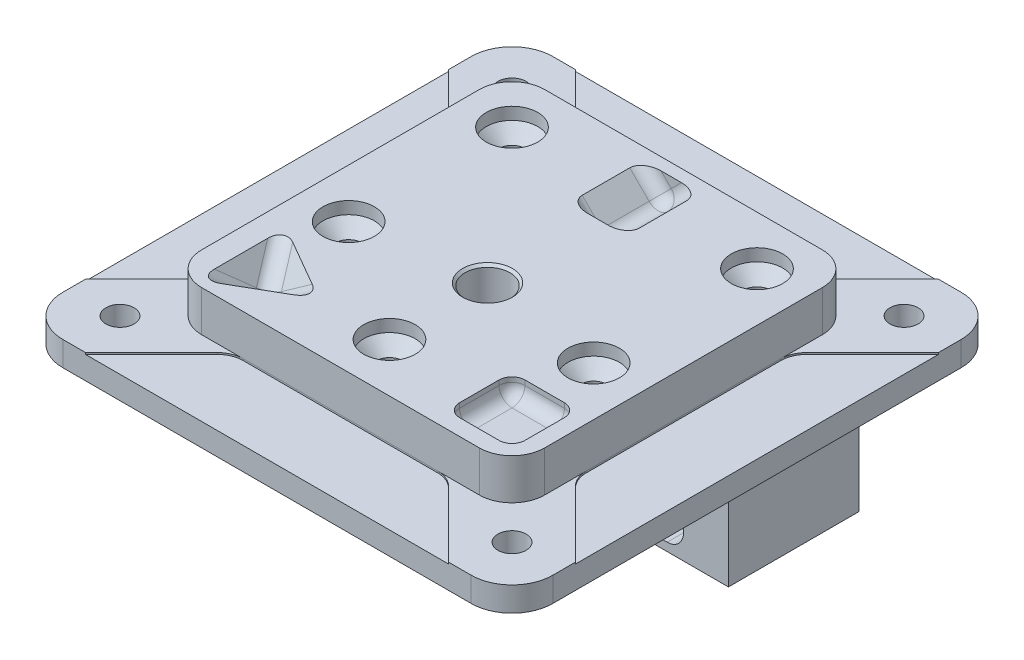
SolidWorks part; units mm, degrees
material "Ti-6Al-4VSolution treated and aged (SS)"
ref_plane "Front" through (0, 0, 0) normal (0, 0, 1) x (1, 0, 0)
ref_plane "Top" through (0, 0, 0) normal (0, 1, 0) x (1, 0, 0)
ref_plane "Right" through (0, 0, 0) normal (1, 0, 0) x (0, 0, -1)
sketch "Sketch6" plane through (0, 0, 0) normal (0, 1, 0) x (1, 0, 0)
  line L0 (8, 0) -> (-8, 0) construction
  line L1 (30, -30) -> (-30, -30)
  line L2 (30, -30) -> (30, 30)
  line L3 (30, 30) -> (-30, 30)
  line L4 (-30, -30) -> (-30, 30)
  line L6 (30, 30) -> (-30, -30) construction
  point P6 (0, 0)
  point P10 (0, 0)
  dimension "D1" = 60
extrude "plate" add sketch "Sketch6" along normal blind 8
sketch "Sketch7" plane through (0, 8, 0) normal (0, 1, 0) x (1, 0, 0)
  line L12 (21, -21) -> (21, 21)
  line L13 (21, 21) -> (-21, 21)
  line L14 (-21, 21) -> (-21, -21)
  line L15 (-21, -21) -> (21, -21)
  line L16 (21, -21) -> (21, 21)
  line L17 (21, 21) -> (-21, 21)
  line L18 (-21, 21) -> (-21, -21)
  line L19 (-21, -21) -> (21, -21)
  line L20 (30, -30) -> (30, 30)
  line L21 (30, 30) -> (-30, 30)
  line L22 (-30, 30) -> (-30, -30)
  line L23 (-30, -30) -> (30, -30)
  line L24 (30, -30) -> (30, 30)
  line L25 (30, 30) -> (-30, 30)
  line L26 (-30, 30) -> (-30, -30)
  line L27 (-30, -30) -> (30, -30)
  dimension "D1" = 9
  dimension "D2" = 0
extrude "top hat" cut sketch "Sketch7" against normal blind 5
sketch "Sketch8" plane through (0, 8, 0) normal (0, 1, 0) x (1, 0, 0)
  line L0 (15, -15) -> (-15, -15) construction
  line L1 (0, -15) -> (0, 15) construction
  line L2 (21, 0) -> (18.1749, 0) construction
  line L3 (21, -21) -> (21, 21) construction
  point P9 (0, 0)
  point P10 (0, -3)
  dimension "D1" = 30
  dimension "D2" = 12
sketch3d "3DSketch1"
  line L0 (-18.1815, 8, 20.5104) -> (-18.1815, 8, 9.4896)
  line L1 (-18.1815, 8, 9.4896) -> (-8.6371, 8, 15)
  line L2 (-8.6371, 8, 15) -> (-18.1815, 8, 20.5104)
  line L3 (-18.1815, 8, 20.5104) -> (-15, 3.5007, 15)
  line L4 (-18.1815, 8, 9.4896) -> (-15, 3.5007, 15)
  line L5 (-8.6371, 8, 15) -> (-15, 3.5007, 15)
  line L6 (-15, 3.5007, 15) -> (-15, 8, 15)
  line L7 (-18.1815, 8, 20.5104) -> (-13.4093, 8, 12.2448)
  line L8 (-8.6371, 8, 15) -> (-18.1815, 8, 15)
  point P8 (-18.1815, 8, 15)
  point P9 (-13.4093, 8, 12.2448)
  dimension "D1" = 4.4993
ref_plane "cube" through (-8.3497, -5.9042, 0) normal (0.8165, 0.5774, 0) x (0, 0, -1)
ref_plane "Plane2" through (0, 0, -15) normal (0, 0, 1) x (1, 0, 0)
sketch "Sketch13" plane through (0, 3, 0) normal (0, 1, 0) x (1, 0, 0)
  line L1 (24, -24) -> (-24, -24)
  line L2 (24, -24) -> (24, 24)
  line L3 (24, 24) -> (-24, 24)
  line L4 (-24, -24) -> (-24, 24)
  line L5 (-24, -24) -> (24, 24) construction
  point P4 (0, 0)
  dimension "D1" = 48
hole_wizard "#8-32 Tapped Hole1" positions "3DSketch3" profile "Sketch16" tap size "#8-32" standard "Ansi Inch" end condition through all
sketch3d "3DSketch3"
  point P0 (-24, 3, -24)
  point P3 (24, 3, -24)
  point P6 (24, 3, 24)
  point P9 (-24, 3, 24)
sketch "Sketch16" plane through (-24, 3, -24) normal (1, 0, 0) x (0, 0, 1)
  line L0 (0, 0) -> (0, 3)
  line L1 (0, 3) -> (1.7272, 3)
  line L2 (1.7272, 3) -> (1.7272, 0)
  line L5 (1.7272, 0) -> (0, 0)
  line L11 (0, -6.35) -> (0, 107.95) construction
  dimension "Thru Tap Drill Dia." = 3.4544
  dimension "Thru Tap Drill Depth" = 3
cosmetic thread "Hole Thread17" parameters "D2"=4.1656
cosmetic thread "Hole Thread18" parameters "D2"=4.1656
cosmetic thread "Hole Thread19" parameters "D2"=4.1656
cosmetic thread "Hole Thread20" parameters "D2"=4.1656
fillet "Fillet2" radius 5 4 edges at (-30, 1.5, -30) (-30, 1.5, 30) (30, 1.5, 30) (30, 1.5, -30)
fillet "Fillet3" radius 4 4 edges at (-21, 5.5, -21) (21, 5.5, -21) (21, 5.5, 21) (-21, 5.5, 21)
sketch "Sketch15" plane through (0, 3, 0) normal (0, 1, 0) x (1, 0, 0)
  line L0 (30, 22.2218) -> (30, -22.2218)
  line L1 (30, 22.2218) -> (21.9299, 14.1518)
  line L2 (30, -22.2218) -> (21.9299, -14.1518)
  line L3 (21, -17) -> (21, 17) construction
  line L4 (21, -11.9067) -> (21, 11.9067)
  line L6 (24, -24) -> (27.8891, -20.1109) construction
  line L7 (21, 0) -> (14.7049, 0) construction
  line L8 (24, -24) -> (-24, 24) construction
  line L9 (24, 24) -> (-24, -24) construction
  line L10 (11.9067, -21) -> (-11.9067, -21)
  line L11 (22.2218, -30) -> (14.1518, -21.9299)
  line L12 (-22.2218, -30) -> (-14.1518, -21.9299)
  line L13 (-22.2218, -30) -> (22.2218, -30)
  line L14 (-30, -22.2218) -> (-30, 22.2218)
  line L15 (-30, 22.2218) -> (-21.9299, 14.1518)
  line L16 (-21, 11.9067) -> (-21, -11.9067)
  line L17 (-30, -22.2218) -> (-21.9299, -14.1518)
  line L18 (22.2218, 30) -> (-22.2218, 30)
  line L19 (-22.2218, 30) -> (-14.1518, 21.9299)
  line L20 (-11.9067, 21) -> (11.9067, 21)
  line L21 (22.2218, 30) -> (14.1518, 21.9299)
  line L23 (-30, 25) -> (-30, -25) construction
  arc A0 (21, 11.9067) -> (21.9299, 14.1518) centre (24.175, 11.9067) cw
  arc A1 (21, -11.9067) -> (21.9299, -14.1518) centre (24.175, -11.9067) ccw
  arc A2 (11.9067, -21) -> (14.1518, -21.9299) centre (11.9067, -24.175) cw
  arc A3 (-11.9067, -21) -> (-14.1518, -21.9299) centre (-11.9067, -24.175) ccw
  arc A4 (-21, 11.9067) -> (-21.9299, 14.1518) centre (-24.175, 11.9067) ccw
  arc A5 (-21, -11.9067) -> (-21.9299, -14.1518) centre (-24.175, -11.9067) cw
  arc A6 (-11.9067, 21) -> (-14.1518, 21.9299) centre (-11.9067, 24.175) cw
  arc A7 (11.9067, 21) -> (14.1518, 21.9299) centre (11.9067, 24.175) ccw
  point P15 (21, -13.2218)
  point P20 (30, 0)
  point P32 (0, -30)
  dimension "D3" = 3.175
  dimension "D1" = 45
  dimension "D2" = 5.5
extrude "Extrude8" cut sketch "Sketch15" against normal blind 0.2
ref_plane "post z center" through (0, 0, 0) normal (0, 0, 1) x (1, 0, 0)
ref_plane "Plane5" through (-11, 0, 0) normal (1, 0, 0) x (0, 0, -1)
sketch "Sketch24" plane through (-11, 0, 0) normal (1, 0, 0) x (0, 0, -1)
  line L0 (0.7631, 2.8) -> (23.4869, 2.8)
  line L1 (-8, 2.8) -> (0.7631, 2.8)
  line L2 (30, 2.8) -> (21.9299, 2.8) construction
  line L3 (22.2218, 2.8) -> (-22.2218, 2.8) construction
  line L5 (-8, -20) -> (-8, 2.8)
  line L6 (0.7631, 2.8) -> (0.7631, -10.5131) construction
  line L7 (0.7631, -10.5131) -> (23.4869, -10.5131) construction
  line L8 (23.4869, -10.5131) -> (23.4869, -20)
  line L9 (23.4869, 2.8) -> (23.4869, -10.5131)
  line L13 (23.4869, -20) -> (-8, -20)
  line L14 (3.5, 2.8) -> (3.5, -10.5131) construction
  circle A0 centre (2.75, -8.5) radius 1.9869 construction
  circle A1 centre (22, -13) radius 1.9869 construction
  point P7 (20.0131, -13)
  point P24 (22, -11.0131)
  point P27 (23.9869, -13)
  point P30 (3.5, -8.5)
  dimension "D2" = 20
  dimension "D9" = 0.75
  dimension "D4" = 13
  dimension "D5" = 19.25
  dimension "D3" = 10.75
  dimension "D6" = 4.5
  dimension "D7" = 0.5
  dimension "D8" = 0.5
  dimension "D12" = 22
extrude "Boss-Extrude1" add sketch "Sketch24" against normal mid plane 16 separate body
sketch "Sketch25" plane through (0, 0, -23.4869) normal (0, 0, -1) x (-1, 0, 0)
  line L0 (6, -13) -> (16, -13) construction
  circle A0 centre (16, -13) radius 1.9869
  circle A1 centre (6, -13) radius 1.9869
  dimension "D1" = 10
extrude "Cut-Extrude1" cut sketch "Sketch25" against normal up to vertex (3.4737 mm away) up to point (-11, -13, -20.0131)
sketch "Sketch26" plane through (0, 0, -23.4869) normal (0, 0, -1) x (-1, 0, 0)
  line L0 (4.5858, -10.5251) -> (8.5, -14.4393)
  line L1 (4.5858, -10.5251) -> (3, -10.5251) construction
  line L2 (8.5, -17) -> (13.5, -17) construction
  line L3 (13.5, -17) -> (13.5, -14.4393)
  line L4 (3, -20) -> (3, 2.8) construction
  line L5 (4.5858, -10.5251) -> (17.4142, -10.5251) construction
  line L6 (6, -13) -> (16, -13) construction
  line L7 (11, -17) -> (11, -13) construction
  line L8 (11, -13) -> (11, -10.5251) construction
  line L9 (10.5, -19) -> (11.5, -19)
  line L10 (4, -9.1109) -> (4, -5.5251)
  line L11 (18, -9.1109) -> (18, -5.5251)
  line L12 (-25, 0) -> (25, 0) construction
  line L13 (6, 0) -> (16, 0)
  line L14 (3, -10.5251) -> (3, -5.5251) construction
  line L15 (3, 0) -> (6, 0) construction
  line L16 (17.4142, -10.5251) -> (19, -10.5251) construction
  line L17 (19, -20) -> (19, 2.8) construction
  line L18 (19, -10.5251) -> (19, -5.5251) construction
  line L19 (16, 0) -> (19, 0) construction
  line L20 (3, -5.5251) -> (3, 0) construction
  line L21 (19, -5.5251) -> (19, 0) construction
  line L22 (4, -5.5251) -> (4, -2)
  line L23 (18, -5.5251) -> (18, -2)
  line L24 (3, -5.5251) -> (4, -5.5251) construction
  line L25 (18, -5.5251) -> (19, -5.5251) construction
  line L26 (8.5, -14.4393) -> (13.5, -14.4393) construction
  line L27 (8.5, -14.4393) -> (8.5, -17)
  line L28 (13.5, -14.4393) -> (17.4142, -10.5251)
  line L29 (19, -20) -> (3, -20) construction
  arc A0 (8.5, -17) -> (10.5, -19) centre (10.5, -17) ccw
  arc A1 (11.5, -19) -> (13.5, -17) centre (11.5, -17) ccw
  arc A2 (4.5858, -10.5251) -> (4, -9.1109) centre (6, -9.1109) cw
  arc A3 (17.4142, -10.5251) -> (18, -9.1109) centre (16, -9.1109) ccw
  arc A4 (16, 0) -> (18, -2) centre (16, -2) cw
  arc A5 (6, 0) -> (4, -2) centre (6, -2) ccw
  point P25 (18, 0)
  point P28 (4, 0)
  dimension "D1" = 2
  dimension "D6" = 5
  dimension "D2" = 4
  dimension "D3" = 0.75
  dimension "D4" = 45
  dimension "D5" = 14
  dimension "D7" = 5
  dimension "D8" = 1
extrude "Cut-Extrude3" cut sketch "Sketch26" against normal up to vertex (23.9687 mm away)
fillet "Fillet4" radius 1 2 edges at (-13.5, -14.4393, -13.4934) (-8.5, -14.4393, -13.4934)
sketch "Sketch28" plane through (0, 0, -23.4869) normal (0, 0, -1) x (-1, 0, 0)
  line L0 (4, -2) -> (4, -9.1109) construction
  line L1 (16, 0) -> (6, 0) construction
  line L2 (18, -9.1109) -> (18, -2) construction
  line L3 (4, -2) -> (4, -9.1109)
  line L4 (3, 2.8) -> (3, -20)
  line L5 (3, -20) -> (19, -20)
  line L6 (19, -20) -> (19, 2.8)
  line L7 (19, 2.8) -> (3, 2.8)
  line L8 (3, 2.8) -> (3, -9.1109)
  line L9 (19, -20) -> (19, 2.8) construction
  line L10 (3, -9.1109) -> (4, -9.1109)
  line L11 (19, 2.8) -> (3, 2.8)
  line L12 (16, 0) -> (6, 0)
  line L13 (18, -9.1109) -> (18, -2)
  line L14 (19, -9.1109) -> (19, 2.8)
  line L15 (18, -9.1109) -> (19, -9.1109)
  arc A0 (6, 0) -> (4, -2) centre (6, -2) ccw construction
  arc A1 (18, -2) -> (16, 0) centre (16, -2) ccw construction
  arc A2 (6, 0) -> (4, -2) centre (6, -2) ccw
  arc A3 (18, -2) -> (16, 0) centre (16, -2) ccw
  dimension "D1" = 0
extrude "Boss-Extrude2" add sketch "Sketch28" along normal up to surface (6.5131 mm away) up to face at (0, 2.2, -30)
hole_wizard "#4-40 Tapped Hole2" positions "Sketch36" profile "Sketch35" tap size "#4-40" standard "Ansi Inch"
sketch "Sketch36" plane through (0, 0, -23.4869) normal (0, 0, -1) x (-1, 0, 0)
  line L3 (6, -17) -> (16, -17) construction
  line L4 (16, -13) -> (16, -17) construction
  line L6 (6, -13) -> (6, -17) construction
  line L9 (16, -20) -> (10.7233, -20) construction
  line L11 (19, -20) -> (3, -20) construction
  line L12 (11, -17) -> (11, -20) construction
  circle A1 centre (16, -17) radius 3 construction
  point P0 (16, -17)
  point P4 (6, -17)
  dimension "D2" = 6
  dimension "D1" = 4
  dimension "D3" = 0
  dimension "D4" = 10
sketch "Sketch35" plane through (-16, -17, -23.4869) normal (1, 0, 0) x (0, 1, 0)
  line L0 (0, 0) -> (0, 8.2742)
  line L1 (0, 8.2742) -> (1.1303, 7.595)
  line L2 (1.1303, 7.595) -> (1.1303, 0)
  line L5 (1.1303, 0) -> (0, 0)
  line L10 (0, 8.2742) -> (-1.1303, 7.595) construction
  line L11 (0, -6.35) -> (0, 107.95) construction
  dimension "Tap Drill Dia." = 2.2606
  dimension "Tap Drill Depth" = 7.595
  dimension "Drill Angle" = 118
cosmetic thread "Hole Thread6" parameters "D1"=5.69, "D2"=2.8448
cosmetic thread "Hole Thread7" parameters "D1"=5.69, "D2"=2.8448
sketch "Sketch44" plane through (-19, 0, 0) normal (-1, 0, 0) x (0, 0, 1)
  line L0 (8, 0) -> (-3.5, 0)
  line L1 (8, 0) -> (8, -20) construction
  line L2 (-7.5, -4) -> (-7.5, -13)
  line L3 (-3.5, -17) -> (8, -17) construction
  line L4 (8, -17) -> (8, -13)
  line L5 (1, -12.5) -> (-2.25, -12.5)
  line L6 (-3.5, -11.25) -> (-3.5, -5.75)
  line L7 (-2.25, -4.5) -> (1, -4.5)
  line L8 (8, -4) -> (8, 0)
  line L9 (-7.5, -8.5) -> (-3.5, -8.5) construction
  line L10 (-3.5, -2) -> (-3.5, -9.1109) construction
  line L12 (-25, 0) -> (25, 0) construction
  line L13 (2.25, -5.75) -> (2.25, -11.25)
  line L14 (8, -4) -> (8, -13)
  line L15 (-7.5, -13) -> (-7.5, -20)
  line L18 (-7.5, -20) -> (8, -20)
  line L19 (8, -20) -> (8, -17)
  arc A0 (-3.5, -5.75) -> (-2.25, -4.5) centre (-2.25, -5.75) cw
  arc A1 (-3.5, 0) -> (-7.5, -4) centre (-3.5, -4) ccw
  arc A2 (-7.5, -13) -> (-3.5, -17) centre (-3.5, -13) ccw construction
  arc A3 (-2.25, -12.5) -> (-3.5, -11.25) centre (-2.25, -11.25) cw
  arc A4 (1, -4.5) -> (2.25, -5.75) centre (1, -5.75) cw
  arc A5 (2.25, -11.25) -> (1, -12.5) centre (1, -11.25) cw
  dimension "D2" = 1.25
  dimension "D5" = 4
  dimension "D1" = 8
  dimension "D3" = 5
  dimension "D4" = 4
extrude "Cut-Extrude7" cut sketch "Sketch44" against normal offset from surface (10.25 mm away) 2.25 up to plane "Plane5" offset beyond the face yes
sketch "Sketch39" plane through (-19, 0, 0) normal (-1, 0, 0) x (0, 0, 1)
  circle A0 centre (-2.75, -8.5) radius 1.9869 construction
  circle A1 centre (-2.75, -8.5) radius 1.9869
extrude "Cut-Extrude4" cut sketch "Sketch39" against normal up to surface (10.25 mm away) up to face at (-8.75, -10.2812, -0.7857)
sketch "Sketch45" plane through (-19, 0, 0) normal (-1, 0, 0) x (0, 0, 1)
  line L5 (2.25, -11.25) -> (2.25, -5.75)
  line L6 (1, -4.5) -> (-2.25, -4.5)
  line L7 (-3.5, -5.75) -> (-3.5, -6.6601)
  line L8 (-3.5, -10.3399) -> (-3.5, -11.25)
  line L9 (-2.25, -12.5) -> (1, -12.5)
  line L10 (2.25, -11.25) -> (2.25, -5.75)
  line L11 (1, -4.5) -> (-2.25, -4.5)
  line L12 (-3.5, -5.75) -> (-3.5, -6.6601)
  line L13 (-3.5, -10.3399) -> (-3.5, -11.25)
  line L14 (-2.25, -12.5) -> (1, -12.5)
  arc A3 (-2.25, -4.5) -> (-3.5, -5.75) centre (-2.25, -5.75) ccw
  arc A4 (-3.5, -10.3399) -> (-3.5, -6.6601) centre (-2.75, -8.5) ccw
  arc A5 (-3.5, -11.25) -> (-2.25, -12.5) centre (-2.25, -11.25) ccw
  arc A6 (-2.25, -4.5) -> (-3.5, -5.75) centre (-2.25, -5.75) ccw
  arc A7 (-3.5, -10.3399) -> (-3.5, -6.6601) centre (-2.75, -8.5) ccw
  arc A8 (-3.5, -11.25) -> (-2.25, -12.5) centre (-2.25, -11.25) ccw
  arc A11 (1, -12.5) -> (2.25, -11.25) centre (1, -11.25) ccw
  arc A12 (1, -12.5) -> (2.25, -11.25) centre (1, -11.25) ccw
  arc A13 (2.25, -5.75) -> (1, -4.5) centre (1, -5.75) ccw
  arc A14 (2.25, -5.75) -> (1, -4.5) centre (1, -5.75) ccw
  dimension "D1" = 0
extrude "Cut-Extrude8" cut sketch "Sketch45" against normal blind 5
sketch "Sketch38" plane through (-3, 0, 0) normal (1, 0, 0) x (0, 0, -1)
  line L6 (30, -9.1109) -> (30, 0)
  line L7 (30, 0) -> (-8, 0)
  line L8 (-8, 0) -> (-8, -20)
  line L9 (-8, -20) -> (23.4869, -20)
  line L10 (23.4869, -20) -> (23.4869, -9.1109)
  line L11 (23.4869, -9.1109) -> (30, -9.1109)
  line L12 (30, -9.1109) -> (30, 0)
  line L13 (30, 0) -> (-8, 0)
  line L14 (-8, 0) -> (-8, -20)
  line L15 (-8, -20) -> (23.4869, -20)
  line L16 (23.4869, -20) -> (23.4869, -9.1109)
  line L17 (23.4869, -9.1109) -> (30, -9.1109)
  dimension "D1" = 0
extrude "Boss-Extrude3" add sketch "Sketch38" along normal up to surface (3 mm away) up to plane "Right"
hole_wizard "#4-40 Tapped Hole1" positions "Sketch47" profile "Sketch46" tap size "#4-40" standard "Ansi Inch"
sketch "Sketch47" plane through (-8.75, 0, 0) normal (-1, 0, 0) x (0, 0, 1)
  line L0 (5.25, -8.5) -> (5.25, -16.5) construction
  line L3 (2.25, -8.5) -> (5.25, -8.5) construction
  line L4 (2.25, -11.25) -> (2.25, -5.75) construction
  line L6 (-7.5, -20) -> (8, -20) construction
  line L7 (8, -20) -> (8, 0) construction
  line L8 (-0.75, -16.5) -> (5.25, -16.5) construction
  point P1 (5.25, -16.5)
  point P30 (-0.75, -16.5)
  dimension "D1" = 8
  dimension "D2" = 3
  dimension "D3" = 3.5
  dimension "D4" = 2.75
  dimension "D5" = 6
sketch "Sketch46" plane through (-8.75, -16.5, 5.25) normal (0, 1, 0) x (0, 0, 1)
  line L0 (0, 0) -> (0, 8.2742)
  line L1 (0, 8.2742) -> (1.1303, 7.595)
  line L2 (1.1303, 7.595) -> (1.1303, 0)
  line L5 (1.1303, 0) -> (0, 0)
  line L10 (0, 8.2742) -> (-1.1303, 7.595) construction
  line L11 (0, -6.35) -> (0, 107.95) construction
  dimension "Tap Drill Dia." = 2.2606
  dimension "Tap Drill Depth" = 7.595
  dimension "Drill Angle" = 118
cosmetic thread "Hole Thread8" parameters "D1"=5.69, "D2"=2.8448
cosmetic thread "Hole Thread9" parameters "D1"=5.69, "D2"=2.8448
mirror "Mirror11" about plane through (0, 0, 0) normal (1, 0, 0) of bodies 179 126 164
combine bodies "Combine1" operation type add bodies to combine 179 140 179
hole_wizard "#10-24 Tapped Hole1" positions "3DSketch2" profile "Sketch12" tap size "#10-24" standard "Ansi Inch"
sketch3d "3DSketch2"
  point P0 (0, 8, 3)
cosmetic thread "Hole Thread1" parameters "D1"=12.7, "D2"=4.826
sketch "Sketch12" plane through (0, 8, 3) normal (1, 0, 0) x (0, 0, 1)
  line L0 (0, 0) -> (0, 17.0188)
  line L1 (0, 17.0188) -> (1.8986, 15.878)
  line L2 (1.8986, 15.878) -> (1.8986, 1.1494)
  line L3 (1.8986, 1.1494) -> (3.048, 0)
  line L5 (3.048, 0) -> (0, 0)
  line L6 (-1.8986, 1.1494) -> (-3.048, 0) construction
  line L10 (0, 17.0188) -> (-1.8987, 15.878) construction
  line L11 (0, -6.35) -> (0, 107.95) construction
  dimension "Tap Drill Dia." = 3.7973
  dimension "Tap Drill Depth" = 15.878
  dimension "Near C'Sink Dia." = 6.096
  dimension "Near C'Sink Angle" = 90
  dimension "Drill Angle" = 118
sketch "Sketch9" plane through (-8.3497, -5.9042, 0) normal (0.8165, 0.5774, 0) x (0, 0, -1)
  line L0 (-20.5104, 17.029) -> (-9.4896, 17.029) construction
  line L1 (-9.4896, 17.029) -> (-15, 11.5186) construction
  line L2 (-20.5104, 17.029) -> (-15, 11.5186) construction
  line L3 (-20.5104, 17.029) -> (-9.4896, 17.029)
  line L4 (-9.4896, 17.029) -> (-15, 11.5186)
  line L5 (-20.5104, 17.029) -> (-15, 11.5186)
extrude "pyr" cut sketch "Sketch9" along normal through all
sketch "Sketch10" plane through (0, 8, 0) normal (0, 1, 0) x (1, 0, 0)
  line L0 (11, -19) -> (19, -11) construction
  line L1 (11, -19) -> (19, -19)
  line L2 (11, -19) -> (11, -11)
  line L3 (11, -11) -> (19, -11)
  line L4 (19, -19) -> (19, -11)
  dimension "D1" = 8
extrude "Extrude6" cut sketch "Sketch10" against normal blind 2.175
sketch "Sketch11" plane through (0, 0, -15) normal (0, 0, 1) x (1, 0, 0)
  line L0 (0, 0) -> (0, 59.9171) construction
  line L1 (17, 8) -> (-17, 8) construction
  line L2 (-7.6651, 12.175) -> (7.6651, 12.175)
  line L3 (7.6651, 12.175) -> (0, 4.5099)
  line L4 (0, 4.5099) -> (-7.6651, 12.175)
  circle A0 centre (0, 9) radius 3.175 construction
  dimension "D1" = 6.35
  dimension "D2" = 1
extrude "Extrude7" cut sketch "Sketch11" against normal mid plane 9
fillet "Fillet1" radius 1.5875 16 edges at (0, 4.5099, -15) (-1.7451, 6.2549, -10.5) (1.7451, 6.2549, -10.5) (-1.7451, 6.2549, -19.5) (1.7451, 6.2549, -19.5) (11, 5.825, 15) (15, 5.825, 19) (19, 5.825, 15) (15, 5.825, 11) (11, 6.9125, 19) (19, 6.9125, 19) (19, 6.9125, 11) (11, 6.9125, 11) (-16.5907, 5.7504, 17.7552) (-11.8185, 5.7504, 15) (-16.5907, 5.7504, 12.2448)
sketch "Sketch62" plane through (0, -20, 0) normal (0, -1, 0) x (1, 0, 0)
  line L0 (2, -4) -> (5.25, -4)
  line L1 (-5.25, 8) -> (5.25, 8)
  line L2 (-5.25, 8) -> (-5.25, -4)
  line L3 (-5.25, -4) -> (-2, -4)
  line L4 (5.25, 8) -> (5.25, -4)
  line L5 (-8.75, -7.5) -> (-5.25, -7.5) construction
  line L6 (-2, -4) -> (-2, -23.4869)
  line L7 (-2, -23.4869) -> (2, -23.4869)
  line L8 (2, -4) -> (2, -23.4869)
  line L9 (-5.25, -7.5) -> (-5.25, -4) construction
  line L10 (-19, -23.4869) -> (19, -23.4869) construction
  line L12 (-8.75, 8) -> (8.75, 8) construction
  line L14 (-4, -30) -> (-4, -23.4869) construction
  line L15 (0, -23.4869) -> (0, 0) construction
  dimension "D2" = 2
  dimension "D3" = 3.5
extrude "Cut-Extrude13" cut sketch "Sketch62" against normal blind 7
fillet "Fillet7" radius 2 2 edges at (5.25, -16.5, -4) (-5.25, -16.5, -4)
fillet "Fillet8" radius 1 2 edges at (2, -16.5, -4) (-2, -16.5, -4)
sketch "Sketch48" plane through (0, 0, -30) normal (0, 0, -1) x (-1, 0, 0)
  line L0 (-30, 0) -> (-30, 3) construction
  line L1 (3, -20) -> (-30, -20)
  line L2 (3, -20) -> (3, 1.5)
  line L3 (30, 8) -> (-30, 8)
  line L4 (-30, -20) -> (-30, 8)
  line L5 (-17, 8) -> (17, 8) construction
  line L6 (19, -20) -> (2, -20) construction
  line L7 (18, -5.5555) -> (19, -5.5555) construction
  line L8 (18, -9.1109) -> (18, -2) construction
  line L9 (19, 0) -> (19, -9.1109) construction
  line L10 (4, -5.5555) -> (3, -5.5555) construction
  line L11 (4, -2) -> (4, -9.1109) construction
  line L12 (19, 0) -> (19, 1.5)
  line L14 (6, 0) -> (16, 0) construction
  line L15 (30, 8) -> (30, 0)
  line L16 (25, 0) -> (30, 0) construction
  line L17 (30, 0) -> (19, 0)
  line L18 (3, 1.5) -> (19, 1.5)
  dimension "D1" = 1.5
extrude "Cut-Extrude9" [suppressed] cut sketch "Sketch48" against normal through all
sketch "Sketch49" [suppressed] plane through (-19, 0, 0) normal (-1, 0, 0) x (0, 0, 1)
  line L0 (30, 0) -> (-3.5, 0) construction
  line L1 (8, 0) -> (30, 0)
  line L2 (8, 0) -> (8, 1.5)
  line L3 (8, 1.5) -> (30, 1.5)
  line L4 (30, 0) -> (30, 1.5)
  line L5 (8, -20) -> (8, 0) construction
extrude "Cut-Extrude10" [suppressed] cut sketch "Sketch49" against normal through all
sketch "Sketch50" plane through (0, 0, 8) normal (0, 0, 1) x (1, 0, 0)
  line L4 (8.75, -20) -> (8.75, 0)
  line L5 (8.75, -20) -> (8.75, 0)
  line L9 (8.75, 0) -> (-8.75, 0)
  line L10 (-8.75, 0) -> (-8.75, -20)
  line L11 (-8.75, -20) -> (-5.25, -20)
  line L13 (-5.25, -20) -> (-5.25, -13)
  line L14 (-5.25, -20) -> (-5.25, -13)
  line L15 (8.75, 0) -> (-8.75, 0)
  line L16 (-8.75, 0) -> (-8.75, -20)
  line L17 (-8.75, -20) -> (-5.25, -20)
  line L18 (-5.25, -13) -> (5.25, -13)
  line L19 (-5.25, -13) -> (5.25, -13)
  line L20 (5.25, -13) -> (5.25, -20)
  line L21 (5.25, -13) -> (5.25, -20)
  line L22 (5.25, -20) -> (8.75, -20)
  line L23 (5.25, -20) -> (8.75, -20)
  dimension "D1" = 0
extrude "Boss-Extrude4" [suppressed] add sketch "Sketch50" along normal blind 6
sketch "Sketch52" [suppressed] plane through (0, 0, 14) normal (0, 0, 1) x (1, 0, 0)
  line L0 (-8.75, -20) -> (-5.75, -20) construction
  line L1 (-3, 1.5) -> (-19, 1.5) construction
  line L2 (-3, 1.5) -> (-3, -20)
  line L3 (-3, -20) -> (-19, -20)
  line L4 (-19, 1.5) -> (-19, -20)
  line L5 (-19, 1.5) -> (-19, 0) construction
  line L6 (-19, 1.5) -> (-19, 13.5)
  line L7 (-19, 13.5) -> (-3, 13.5)
  line L8 (-3, 13.5) -> (-3, 1.5)
  dimension "D1" = 12
extrude "Boss-Extrude5" [suppressed] add sketch "Sketch52" along normal blind 10
fillet "Fillet5" [suppressed] radius 4
fillet "Fillet6" [suppressed] radius 4
hole_wizard "M3x0.5 Tapped Hole1" positions "Sketch54" profile "Sketch53" tap size "M3x0.5" standard "Ansi Metric"
sketch "Sketch54" [suppressed] plane through (0, 0, 24) normal (0, 0, 1) x (1, 0, 0)
  line L0 (-11, 13.5) -> (-11, -20) construction
  line L2 (-19, -20) -> (-3, -20) construction
  line L4 (-3, 13.5) -> (-19, 13.5) construction
  line L5 (-11, 3) -> (-3, 3) construction
  line L6 (-3, -20) -> (-3, 13.5) construction
  line L8 (-11, 8) -> (-3, 8) construction
  point P0 (-11, -4)
  point P1 (-11, -13)
  dimension "D1" = 16
  dimension "D2" = 5
  dimension "D3" = 7
  dimension "D4" = 9
cosmetic thread "Hole Thread10" [suppressed] parameters "D2"=3
cosmetic thread "Hole Thread11" [suppressed] parameters "D2"=3
sketch "Sketch53" plane through (-11, -4, 24) normal (1, 0, 0) x (0, -1, 0)
  line L0 (0, 0) -> (0, 10)
  line L1 (0, 10) -> (1.25, 10)
  line L2 (1.25, 10) -> (1.25, 0)
  line L5 (1.25, 0) -> (0, 0)
  line L11 (0, -6.35) -> (0, 107.95) construction
  dimension "Thru Tap Drill Dia." = 2.5
  dimension "Thru Tap Drill Depth" = 10
sketch "Sketch55" [suppressed] plane through (0, 0, 24) normal (0, 0, 1) x (1, 0, 0)
  circle A0 centre (-11, 8) radius 1.2575
  circle A1 centre (-11, 3) radius 1.2575
  dimension "D1" = 2.515
extrude "Cut-Extrude11" [suppressed] cut sketch "Sketch55" against normal through all
sketch "Sketch56" [suppressed] plane through (0, 0, -30) normal (0, 0, -1) x (-1, 0, 0)
  line L0 (3, 1.5) -> (19, 1.5) construction
  line L1 (4, -2) -> (18, -2)
  line L2 (4, -2) -> (4, 1.5)
  line L3 (4, 1.5) -> (18, 1.5)
  line L4 (18, -2) -> (18, 1.5)
  line L5 (18, -9.1109) -> (18, -2) construction
extrude "Cut-Extrude12" [suppressed] cut sketch "Sketch56" against normal up to surface (6.5131 mm away)
ref_plane "Plane6" through (0, 3, 0) normal (0, 1, 0) x (-1, 0, 0)
split "Split1" trim tools "Plane6" bodies to split 192 resulting bodies 187 188
hole_wizard "CSK for M3 Flat Head Machine Screw1" positions "Sketch58" profile "Sketch57" countersink size "M3" standard "Ansi Metric"
sketch "Sketch58" plane through (0, 8, 0) normal (0, 1, 0) x (-1, 0, 0)
  line L0 (-15, -15) -> (15, -15)
  line L1 (15, -15) -> (15, 5)
  line L2 (15, 5) -> (-15, 5)
  line L3 (-15, 5) -> (-15, -15)
  line L5 (0, 5) -> (0, 15)
  line L8 (-11.9067, 21) -> (11.9067, 21) construction
  line L11 (0, 15) -> (0, 21)
  line L15 (15, 5) -> (21, 5)
  line L20 (21, -17) -> (21, 17) construction
  line L21 (15, -15) -> (15, -21)
  line L22 (-17, -21) -> (17, -21) construction
  point P0 (-15, -15)
  point P1 (15, -15)
  point P3 (0, 15)
  point P5 (-15, 5)
  point P7 (15, 5)
  dimension "D1" = 6
  dimension "D2" = 10
sketch "Sketch57" plane through (15, 8, -15) normal (1, 0, 0) x (0, 0, 1)
  line L0 (0, 0) -> (0, 5.9604)
  line L1 (0, 5.9604) -> (1.6, 4.999)
  line L2 (1.6, 4.999) -> (1.6, 3.05)
  line L3 (1.6, 3.05) -> (3.15, 1.5)
  line L4 (3.15, 1.5) -> (3.15, 0)
  line L6 (3.15, 0) -> (0, 0)
  line L7 (-1.6, 3.05) -> (-3.15, 1.5) construction
  line L10 (0, 5.9604) -> (-1.6, 4.999) construction
  line L11 (0, -6.35) -> (0, 107.95) construction
  dimension "Hole Dia." = 3.2
  dimension "Hole Depth" = 4.999
  dimension "C'Sink Dia." = 6.3
  dimension "C'Sink Angle" = 90
  dimension "Drill Angle" = 118
  dimension "Head Clearance" = 1.5
hole_wizard "M3x0.5 Tapped Hole2" positions "Sketch60" profile "Sketch61" tap size "M3x0.5" standard "Ansi Metric" end condition up to next
sketch "Sketch60" plane through (23.4465, 3, -19.2674) normal (0, 1, 0) x (-1, 0, 0)
  point P1 (8.4465, 24.2674)
  point P4 (38.4465, 24.2674)
  point P7 (38.4465, 4.2674)
  point P10 (8.4465, 4.2674)
  point P15 (23.4465, 34.2674)
sketch "Sketch61" plane through (15, 3, 5) normal (1, 0, 0) x (0, 0, 1)
  line L0 (0, 0) -> (0, 3)
  line L1 (0, 3) -> (1.25, 3)
  line L2 (1.25, 3) -> (1.25, 0)
  line L5 (1.25, 0) -> (0, 0)
  line L11 (0, -6.35) -> (0, 107.95) construction
  dimension "Thru Tap Drill Dia." = 2.5
  dimension "Thru Tap Drill Depth" = 3
cosmetic thread "Hole Thread12" parameters "D1"=0, "D2"=3.5
cosmetic thread "Hole Thread13" parameters "D1"=0, "D2"=3.5
cosmetic thread "Hole Thread14" parameters "D1"=0, "D2"=3.5
cosmetic thread "Hole Thread15" parameters "D1"=0, "D2"=3.5
cosmetic thread "Hole Thread16" parameters "D1"=0, "D2"=3.5
delete or keep bodies "Body-Delete1" [suppressed] type delete bodies bodies 189
delete or keep bodies "Body-Delete2" [suppressed] type delete bodies bodies 191
sketch "Sketch63" plane through (0, 8, 0) normal (0, 1, 0) x (1, 0, 0)
  circle A0 centre (0, -3) radius 2.75
  circle A1 centre (0, -3) radius 3.048 construction
  dimension "D1" = 5.5
extrude "Cut-Extrude14" cut sketch "Sketch63" against normal through all
equation "\"actual_bearing_ball_diam\"= 5/32*25.4"
equation "\"gap_tol\"= 0.005"
equation "\"bearing_ball_diam\"= \"actual_bearing_ball_diam\" + \"gap_tol\""
